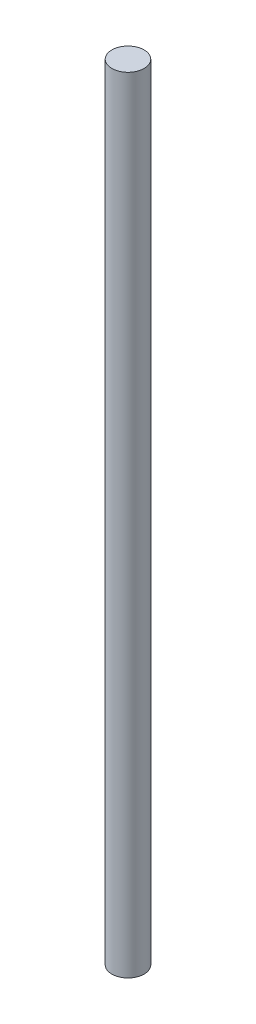
SolidWorks part; units mm, degrees
material "AISI 304"
ref_plane "Front Plane" through (0, 0, 0) normal (0, 0, 1) x (1, 0, 0)
ref_plane "Top Plane" through (0, 0, 0) normal (0, 1, 0) x (1, 0, 0)
ref_plane "Right Plane" through (0, 0, 0) normal (1, 0, 0) x (0, 0, -1)
sketch "Sketch1" plane through (0, 0, 0) normal (0, 1, 0) x (1, 0, 0)
  circle A0 centre (0, 0) radius 3
  dimension "D1" = 6
extrude "Boss-Extrude1" add sketch "Sketch1" along normal blind 146
